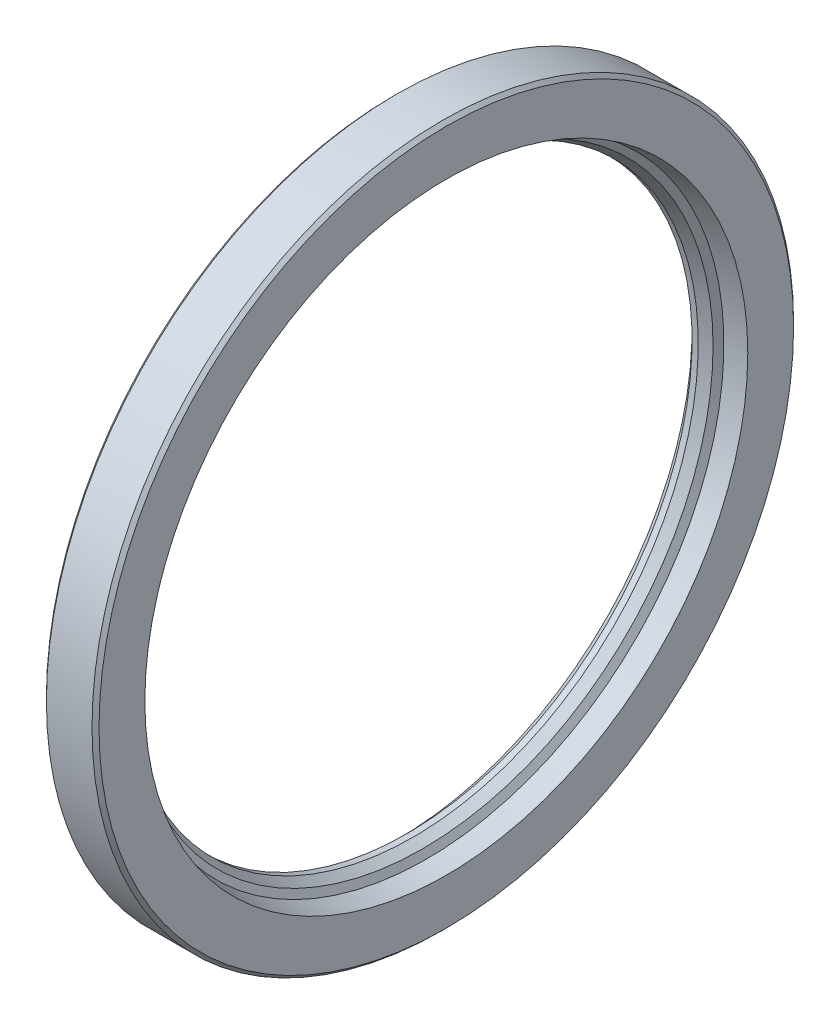
SolidWorks part; units mm, degrees
other "PR" parameters "D2"=1.0482, "D14"=1.4063, "D1"=7, "D3"=3, "D4"=3, "D5"=0.7043, "D6"=7, "D7"=7, "D8"=7, "D9"=2.6946, "D10"=4.1, "D11"=6.2, "D12"=6.2, "D13"=1
ref_plane "Спереди" through (0, 0, 0) normal (0, 0, 1) x (1, 0, 0)
ref_plane "Сверху" through (0, 0, 0) normal (0, 1, 0) x (1, 0, 0)
ref_plane "Справа" through (0, 0, 0) normal (1, 0, 0) x (0, 0, -1)
sketch "main" plane through (0, 0, 0) normal (0, 0, 1) x (1, 0, 0)
  line L0 (-6, 0) -> (6, 0) construction
  line L1 (5.2, 80) -> (6, 79.2) construction
  line L2 (-6, 80) -> (6, 80)
  line L3 (-6, 80) -> (-6, 65)
  line L4 (-6, 65) -> (6, 65)
  line L5 (6, 80) -> (6, 65)
  line L6 (6, 79.2) -> (6, 80) construction
  line L7 (6, 80) -> (5.2, 80) construction
  dimension "d1" = 130
  dimension "d2" = 160
  dimension "b" = 12
  dimension "c" = 0.8
sketch "eq" plane through (0, 0, 0) normal (0, 0, 1) x (1, 0, 0)
  line L0 (-6, 77.1875) -> (-6, 79.2)
  line L1 (-6, 80) -> (-5.2, 80) construction
  line L2 (6, 80) -> (6, 79.2) construction
  line L3 (6, 68.75) -> (1.5, 67.8052)
  line L4 (1.5, 67.8052) -> (0.5941, 66.2361)
  line L5 (0.5941, 66.2361) -> (-1.5469, 65)
  line L6 (-6, 65) -> (6, 65) construction
  line L7 (-1.5469, 65) -> (-2.9531, 65)
  line L8 (-2.9531, 65) -> (-5.0625, 67.1094)
  line L9 (-5.0625, 67.1094) -> (-5.0625, 69.4531)
  line L10 (-5.0625, 69.4531) -> (-3.6562, 69.4531)
  line L11 (-3.6562, 69.4531) -> (-3.6562, 68.75)
  line L12 (-0.8437, 68.75) -> (0.375, 69.0059)
  line L13 (0.375, 69.0059) -> (0.375, 74.8834)
  line L14 (-0.7871, 76.2683) -> (-6, 77.1875)
  line L15 (-6, 79.2) -> (-6, 80) construction
  line L16 (-5.2, 80) -> (5.2, 80)
  line L17 (5.2, 80) -> (6, 80) construction
  line L18 (6, 79.2) -> (6, 68.75)
  line L19 (5.2, 80) -> (6, 79.2)
  line L20 (-5.2, 80) -> (-6, 79.2)
  line L21 (5.2, 80) -> (6, 79.2) construction
  line L22 (-6, 80) -> (6, 80) construction
  line L23 (6, 80) -> (6, 65) construction
  line L24 (-6, 80) -> (-6, 65) construction
  line L25 (-6, 72.5) -> (-6, 65) construction
  line L26 (-6, 68.75) -> (1.5, 68.75) construction
  line L27 (-2.25, 68.75) -> (-2.25, 65) construction
  line L28 (0.375, 71.9447) -> (6, 71.9447) construction
  line L30 (1.5, 71.9447) -> (4.875, 71.9447) construction
  arc A0 (-3.6562, 68.75) -> (-0.8437, 68.75) centre (-2.25, 68.75) ccw
  circle A1 centre (-2.25, 68.75) radius 1.4062 construction
  arc A2 (0.375, 74.8834) -> (-0.7871, 76.2683) centre (-1.0313, 74.8834) ccw
  point P41 (3.1875, 71.9447)
  dimension "D2" = 2.8125
  dimension "D1" = 3.75
  dimension "D3" = 0.7031
  dimension "D4" = 0.9375
  dimension "D5" = 1.4063
  dimension "D6" = 45
  dimension "D7" = 30
  dimension "D8" = 60
  dimension "D9" = 1.4063
  dimension "D10" = 5.625
  dimension "D11" = 10
  dimension "D12" = 2.8125
  dimension "D13" = 3.375
revolve "KR" add sketch "eq" angle 360 about L0
sketch "eq1" plane through (0, 0, 0) normal (0, 0, 1) x (1, 0, 0)
  circle A0 centre (-2.25, 68.75) radius 1.4062 construction
  circle A1 centre (-2.25, 68.75) radius 1.4062
revolve "PR" add sketch "eq1" angle 360 about L0
sketch "a" plane through (0, 0, 0) normal (0, 0, 1) x (1, 0, 0)
  line L0 (1.5, 67.8052) -> (4.875, 68.5138)
  line L1 (6, 68.75) -> (1.5, 67.8052) construction
  line L2 (4.875, 68.5138) -> (4.875, 67.8052)
  line L3 (4.875, 67.8052) -> (6, 65)
  line L4 (6, 65) -> (4.5937, 65)
  line L5 (-6, 65) -> (6, 65) construction
  line L6 (4.5937, 65) -> (1.5, 67.8052)
  line L7 (-1.5469, 65) -> (-2.9531, 65) construction
revolve "A_" [suppressed] add sketch "a" angle 360 about L0
sketch "aa" plane through (0, 0, 0) normal (0, 0, 1) x (1, 0, 0)
  line L0 (4.875, 68.5138) -> (4.875, 67.8052) construction
  line L1 (4.875, 67.8052) -> (6, 65) construction
  line L2 (4.875, 76.2683) -> (4.875, 67.8052)
  line L3 (4.875, 67.8052) -> (6, 65)
  line L4 (4.875, 76.2683) -> (6, 76.2683)
  line L5 (6, 76.2683) -> (6, 65)
  line L6 (6, 80) -> (6, 65) construction
revolve "AA_" [suppressed] cut sketch "aa" angle 360 about L0
equation "\"D2@eq\" = \"D1@eq\" * 0.75"
equation "\"D3@eq\" = \"D2@eq\" / 4"
equation "\"D4@eq\" = \"D1@eq\" / 4"
equation "\"D5@eq\" = \"D2@eq\" / 2"
equation "\"D9@eq\" = \"D2@eq\" / 2"
equation "\"D10@eq\" = \"D1@eq\" * 1.5"
equation "\"D12@eq\" = \"D1@eq\" * 0.75"
equation "\"D13@eq\"=\"D10@eq\"*0.6"
equation "\"D14@eq\"=\"D9@eq\""
